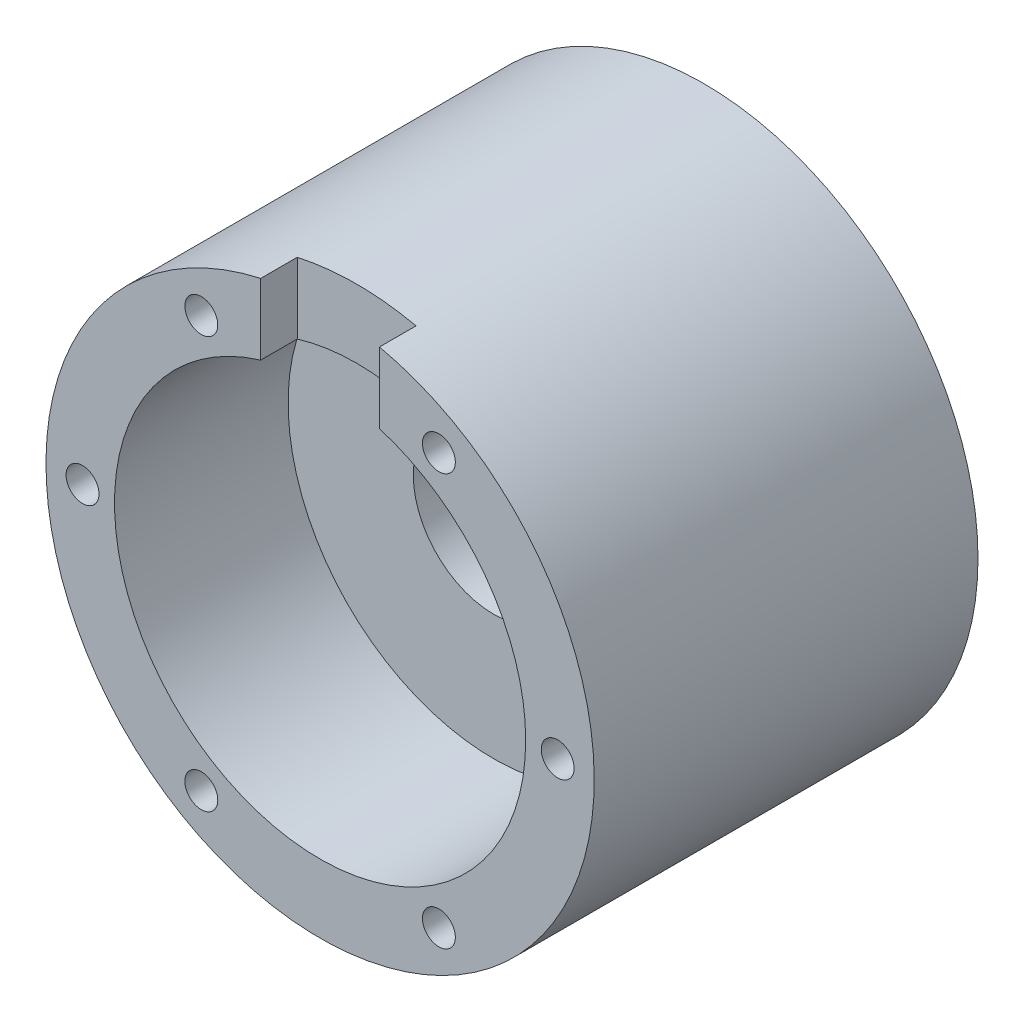
SolidWorks part; units mm, degrees
ref_plane "정면" through (0, 0, 0) normal (0, 0, 1) x (1, 0, 0)
ref_plane "윗면" through (0, 0, 0) normal (0, 1, 0) x (1, 0, 0)
ref_plane "우측면" through (0, 0, 0) normal (1, 0, 0) x (0, 0, -1)
sketch "스케치1" plane through (0, 0, 0) normal (0, 0, 1) x (1, 0, 0)
  circle A0 centre (0, 0) radius 15
  circle A1 centre (0, 0) radius 4.4
  circle A2 centre (0, 6.25) radius 1.45
  point P6 (0, 0)
  dimension "D1" = 30
  dimension "D2" = 8.8
  dimension "D3" = 2.9
  dimension "D4" = 6.25
extrude "보스-돌출1" add sketch "스케치1" along normal blind 21
sketch "스케치2" plane through (0, 0, 0) normal (0, 0, -1) x (-1, 0, 0)
  circle A0 centre (0, 0) radius 7.7
  dimension "D1" = 15.4
extrude "컷-돌출1" cut sketch "스케치2" against normal blind 4
sketch "스케치3" plane through (0, 0, 21) normal (0, 0, 1) x (1, 0, 0)
  circle A0 centre (0, 0) radius 11.25
  dimension "D1" = 22.5
extrude "컷-돌출2" cut sketch "스케치3" against normal blind 9.5
sketch "스케치4" plane through (0, 0, 21) normal (0, 0, 1) x (1, 0, 0)
  line L0 (0, 0) -> (13, 0) construction
  line L1 (0, 0) -> (6.5, -11.2583) construction
  circle A0 centre (13, 0) radius 0.9
  circle A1 centre (6.5, -11.2583) radius 0.9
  circle A2 centre (-6.5, -11.2583) radius 0.9
  circle A3 centre (-13, 0) radius 0.9
  circle A4 centre (-6.5, 11.2583) radius 0.9
  circle A5 centre (6.5, 11.2583) radius 0.9
  dimension "D1" = 1.8
  dimension "D2" = 13
  dimension "D4" = 60
  dimension "D3" = 6
extrude "컷-돌출3" cut sketch "스케치4" against normal blind 4
sketch "스케치5" plane through (0, 0, 21) normal (0, 0, 1) x (1, 0, 0)
  line L1 (3.25, 7.5) -> (-3.25, 7.5)
  line L2 (3.25, 7.5) -> (3.25, 16.5)
  line L3 (3.25, 16.5) -> (-3.25, 16.5)
  line L4 (-3.25, 7.5) -> (-3.25, 16.5)
  line L5 (3.25, 7.5) -> (-3.25, 16.5) construction
  line L6 (3.25, 16.5) -> (-3.25, 7.5) construction
  point P0 (0, 12)
  dimension "D1" = 12
  dimension "D2" = 9
  dimension "D3" = 6.5
extrude "컷-돌출4" cut sketch "스케치5" against normal blind 2
